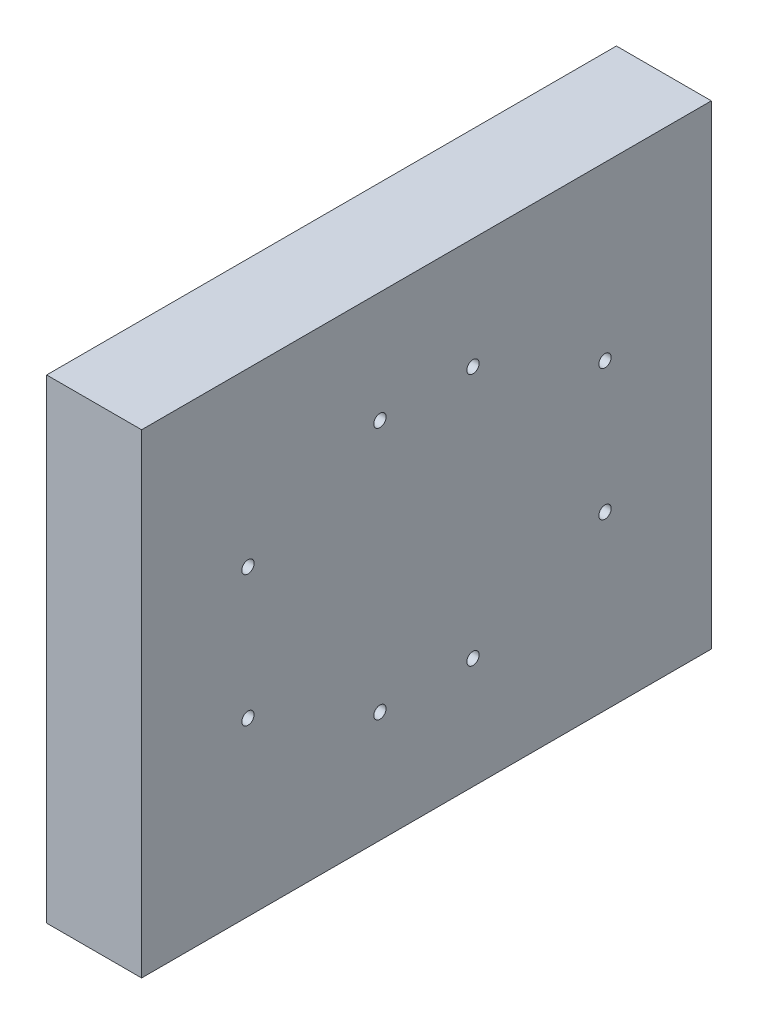
SolidWorks part; units mm, degrees
ref_plane "Front Plane" through (0, 0, 0) normal (0, 0, 1) x (1, 0, 0)
ref_plane "Top Plane" through (0, 0, 0) normal (0, 1, 0) x (1, 0, 0)
ref_plane "Right Plane" through (0, 0, 0) normal (1, 0, 0) x (0, 0, -1)
sketch "Sketch1" plane through (0, 0, 0) normal (1, 0, 0) x (0, 0, -1)
  line L1 (0, 0) -> (152.4, 0)
  line L2 (0, 0) -> (0, 127)
  line L3 (0, 127) -> (152.4, 127)
  line L4 (152.4, 0) -> (152.4, 127)
  circle A8 centre (28.448, 81.026) radius 1.651
  circle A9 centre (28.448, 45.974) radius 1.651
  circle A10 centre (123.952, 81.026) radius 1.651
  circle A11 centre (123.952, 45.974) radius 1.651
  circle A12 centre (63.754, 97.282) radius 1.651
  circle A13 centre (88.646, 97.282) radius 1.651
  circle A14 centre (63.754, 29.718) radius 1.651
  circle A15 centre (88.646, 29.718) radius 1.651
  dimension "D3" = 3.302
  dimension "D4" = 3.302
  dimension "D5" = 3.302
  dimension "D6" = 3.302
  dimension "D9" = 28.448
  dimension "D10" = 45.974
  dimension "D11" = 28.448
  dimension "D7" = 45.974
  dimension "D8" = 28.448
  dimension "D12" = 45.974
  dimension "D13" = 28.448
  dimension "D14" = 45.974
  dimension "D15" = 3.302
  dimension "D16" = 3.302
  dimension "D17" = 3.302
  dimension "D18" = 3.302
  dimension "D19" = 29.718
  dimension "D20" = 63.754
  dimension "D21" = 63.754
  dimension "D22" = 29.718
  dimension "D24" = 63.754
  dimension "D25" = 63.754
  dimension "D1" = 152.4
  dimension "D2" = 127
  dimension "D23" = 29.718
  dimension "D26" = 29.718
extrude "Boss-Extrude1" add sketch "Sketch1" along normal blind 25.4
